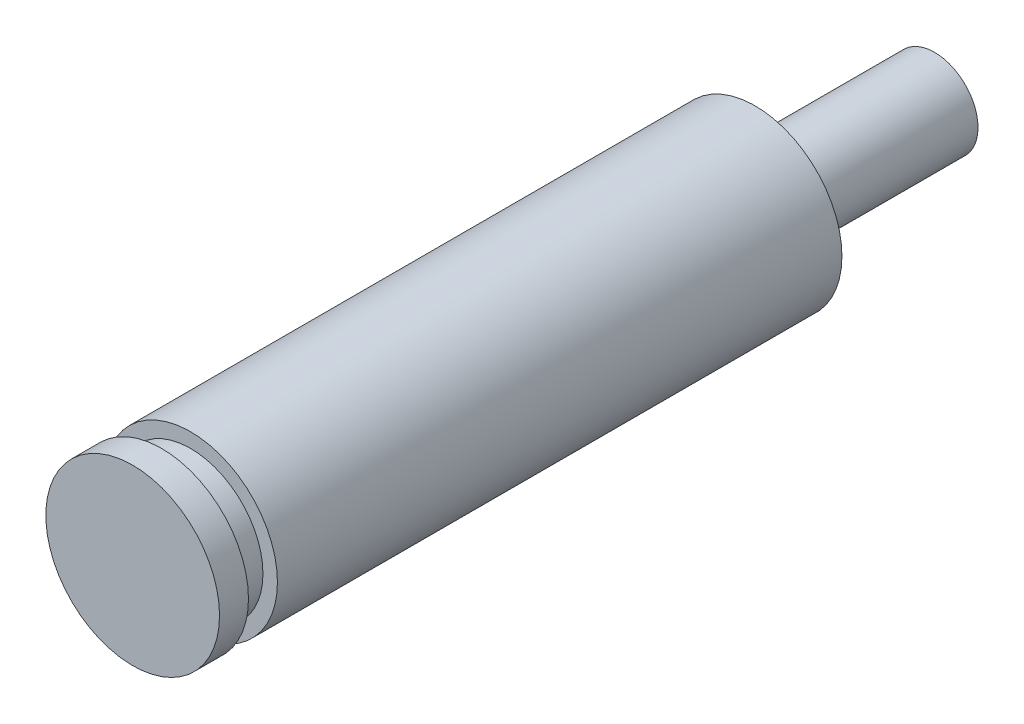
SolidWorks part; units mm, degrees
ref_plane "Front Plane" through (0, 0, 0) normal (0, 0, 1) x (1, 0, 0)
ref_plane "Top Plane" through (0, 0, 0) normal (0, 1, 0) x (1, 0, 0)
ref_plane "Right Plane" through (0, 0, 0) normal (1, 0, 0) x (0, 0, -1)
sketch "Sketch1" plane through (0, 0, 0) normal (0, 1, 0) x (1, 0, 0)
  line L0 (0, 0) -> (0, 27.7)
  line L1 (0, 27.7) -> (1.5, 27.7)
  line L2 (1.5, 27.7) -> (1.5, 21.5)
  line L3 (1.5, 21.5) -> (3, 21.5)
  line L4 (3, 21.5) -> (3, 2)
  line L5 (3, 2) -> (2.5, 2)
  line L6 (2.5, 2) -> (2.5, 1)
  line L7 (2.5, 1) -> (3, 1)
  line L8 (3, 1) -> (3, 0)
  line L9 (3, 0) -> (0, 0)
  point P8 (3.2408, 23.6136)
  dimension "D1" = 3
  dimension "D2" = 27.7
  dimension "D3" = 2.5
  dimension "D4" = 1
  dimension "D5" = 1
  dimension "D6" = 21.5
  dimension "D7" = 1.5
revolve "Revolve1" add sketch "Sketch1" angle 360 about L0
